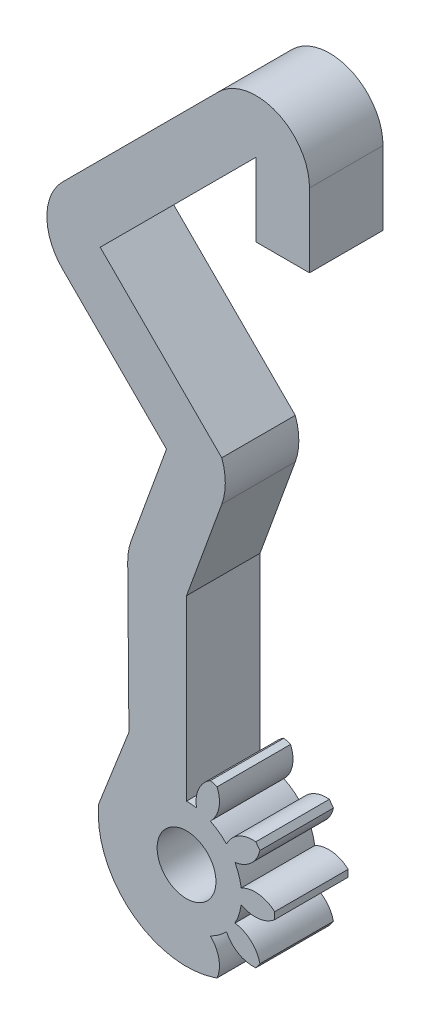
SolidWorks part; units mm, degrees
ref_plane "Ön Düzlem" through (0, 0, 0) normal (0, 0, 1) x (1, 0, 0)
ref_plane "Üst Düzlem" through (0, 0, 0) normal (0, 1, 0) x (1, 0, 0)
ref_plane "Sağ Düzlem" through (0, 0, 0) normal (1, 0, 0) x (0, 0, -1)
sketch "Sketch1" plane through (0, 0, 0) normal (0, 0, 1) x (1, 0, 0)
  line L0 (-2.5201, 12.1174) -> (-2.5201, 6.2698)
  line L1 (-2.5201, 6.2698) -> (-0.666, 0.5635)
  line L11 (-2.5201, 12.1174) -> (-2.5201, 22.1174)
  line L14 (-0.1242, 28.7) -> (-2.5201, 22.1174)
  line L15 (-3.883, 30.0681) -> (-10.9541, 37.1392)
  line L16 (-0.1242, 31.4362) -> (-8.3907, 39.7026)
  line L17 (-8.3907, 39.7026) -> (2.2159, 50.3092)
  line L18 (2.2159, 50.3092) -> (2.2159, 45.3092)
  line L19 (2.2159, 45.3092) -> (5.8412, 45.3092)
  line L20 (-10.9541, 42.266) -> (-0.3475, 52.8726)
  line L21 (5.8412, 50.3092) -> (5.8412, 45.3092)
  line L22 (-3.883, 30.0681) -> (-6.2789, 23.4855)
  line L25 (-6.5201, 22.1174) -> (-6.4379, 12.1178)
  line L26 (-6.4379, 12.1178) -> (-8.4887, 6.8835)
  arc A0 (-0.666, 0.5635) -> (-8.4887, 6.8835) centre (-2.5201, 6.2698) cw
  arc A1 (-0.1242, 28.7) -> (-0.1242, 31.4362) centre (-3.883, 30.0681) ccw
  arc A5 (-10.9541, 37.1392) -> (-10.9541, 42.266) centre (-8.3907, 39.7026) cw
  arc A6 (-0.3475, 52.8726) -> (5.8412, 50.3092) centre (2.2159, 50.3092) cw
  arc A7 (-6.2789, 23.4855) -> (-6.5201, 22.1174) centre (-2.5201, 22.1174) ccw
extrude "Boss-Extrude1" add sketch "Sketch1" along normal blind 5 contours L0 L1 A0 L26 L25 A7 L22 L15 A5 L20 A6 L21 L19 L18 L17 L16 A1 L14 L11
sketch "Sketch2" plane through (0, 0, 5) normal (0, 0, 1) x (1, 0, 0)
  line L0 (-0.666, 0.5635) -> (-0.4442, 0.6404)
  line L1 (2.1923, 2.5559) -> (2.4683, 2.9358)
  line L2 (3.4753, 6.0351) -> (3.4753, 6.5046)
  line L3 (-0.4442, 11.8993) -> (-0.8907, 12.0443)
  line L4 (-2.5201, 8.2698) -> (-2.5201, 10.0188)
  line L5 (2.4683, 9.6039) -> (2.1923, 9.9838)
  line L6 (-0.666, 0.5635) -> (-1.9021, 4.3677)
  arc A0 (-2.5201, 10.0188) -> (-1.8392, 9.9565) centre (-2.5201, 6.2698) cw
  arc A1 (-0.4442, 0.6404) -> (-0.9041, 2.887) centre (-2.2795, 1.4351) ccw
  arc A2 (-1.9021, 4.3677) -> (-2.5201, 8.2698) centre (-2.5201, 6.2698) ccw
  arc A3 (2.1923, 2.5559) -> (0.1977, 3.6875) centre (2.0037, 4.547) cw
  arc A4 (2.4683, 2.9358) -> (0.7757, 4.483) centre (0.5163, 2.4999) ccw
  arc A5 (3.4753, 6.0351) -> (1.1965, 5.7782) centre (2.1524, 7.535) cw
  arc A6 (1.1965, 6.7614) -> (3.4753, 6.5046) centre (2.1524, 5.0046) cw
  arc A7 (2.4683, 9.6039) -> (0.7757, 8.0567) centre (0.5163, 10.0398) cw
  arc A8 (2.1923, 9.9838) -> (0.1977, 8.8521) centre (2.0037, 7.9927) ccw
  arc A9 (-0.4442, 11.8993) -> (-0.9041, 9.6526) centre (-2.2795, 11.1046) cw
  arc A10 (-0.8907, 12.0443) -> (-1.8392, 9.9565) centre (0.127, 10.3227) ccw
  arc A11 (-0.9041, 9.6526) -> (0.1977, 8.8521) centre (-2.5201, 6.2698) cw
  arc A12 (0.7757, 8.0567) -> (1.1965, 6.7614) centre (-2.5201, 6.2698) cw
  arc A13 (1.1965, 5.7782) -> (0.7757, 4.483) centre (-2.5201, 6.2698) cw
  arc A14 (0.1977, 3.6875) -> (-0.9041, 2.887) centre (-2.5201, 6.2698) cw
  point P32 (0, 0)
extrude "Boss-Extrude2" add sketch "Sketch2" against normal up to surface (5 mm away) up to face at (-2.9907, 30.3852, 0)
sketch "Sketch3" plane through (0, 0, 5) normal (0, 0, 1) x (1, 0, 0)
  circle A0 centre (-2.5201, 6.2698) radius 2
extrude "Cut-Extrude1" cut sketch "Sketch3" against normal up to next
